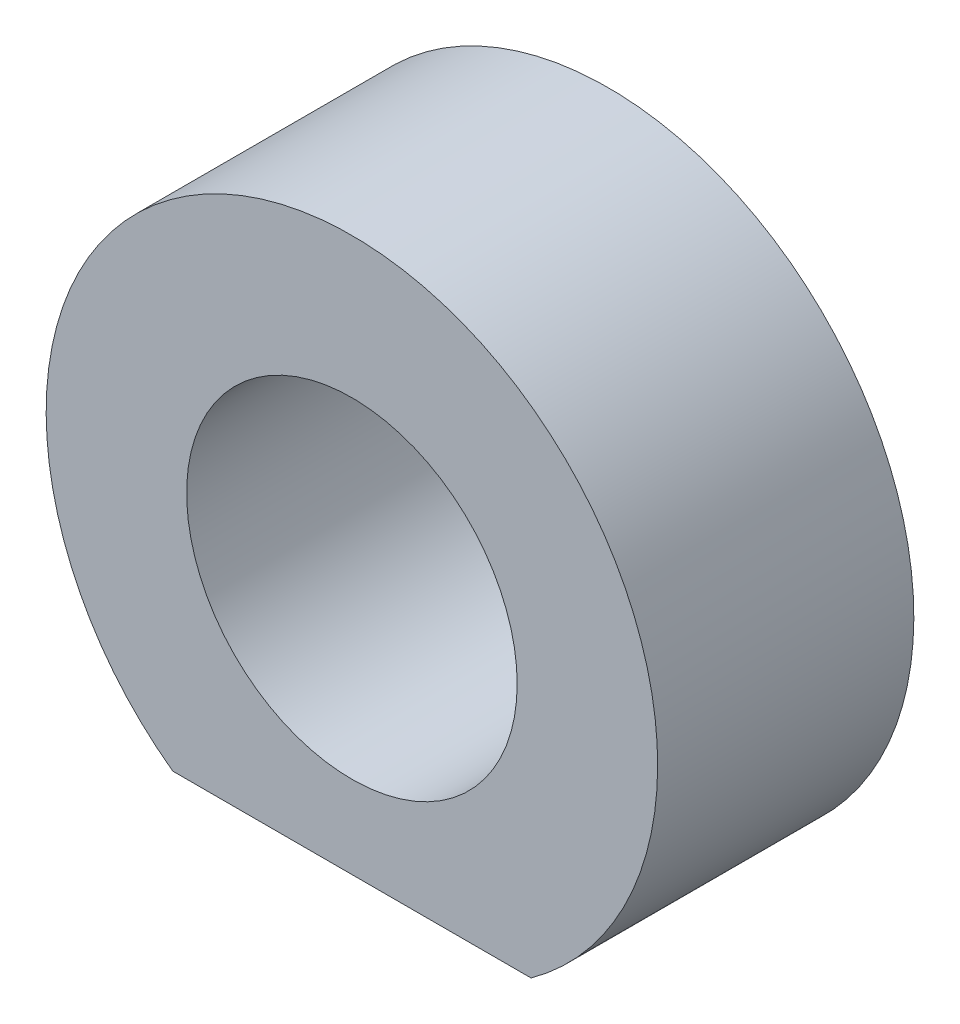
SolidWorks part; units mm, degrees
ref_plane "Front Plane" through (0, 0, 0) normal (0, 0, 1) x (1, 0, 0)
ref_plane "Top Plane" through (0, 0, 0) normal (0, 1, 0) x (1, 0, 0)
ref_plane "Right Plane" through (0, 0, 0) normal (1, 0, 0) x (0, 0, -1)
sketch "Sketch1" plane through (0, 0, 0) normal (0, 0, 1) x (1, 0, 0)
  line L0 (0, -23.3211) -> (0, -18.5) construction
  line L1 (-24.2602, 0) -> (25.6689, 0) construction
  line L2 (-10.84, -14.9915) -> (10.84, -14.9915)
  line L3 (0, -14.9915) -> (0, 23.3211) construction
  circle A0 centre (0, 0) radius 10
  arc A1 (10.84, -14.9915) -> (-10.84, -14.9915) centre (0, 0) ccw
  point P7 (0, 0)
  dimension "D1" = 20
  dimension "D2" = 37
  dimension "D3" = 21.68
extrude "Boss-Extrude1" add sketch "Sketch1" along normal blind 15.5
hole_wizard "Ø2.0 (2) Diameter Hole1" positions "Sketch3" profile "Sketch4" hole size "Ø2.0" standard "ISO"
sketch "Sketch3" plane through (0, -14.9915, 0) normal (0, -1, 0) x (-1, 0, 0)
  point P0 (0, -7.75)
  dimension "D1" = 7.75
sketch "Sketch4" plane through (0, -14.9915, 7.75) normal (1, 0, 0) x (0, 0, -1)
  line L0 (0, 0) -> (0, 2.6009)
  line L1 (0, 2.6009) -> (1, 2)
  line L2 (1, 2) -> (1, 0)
  line L5 (1, 0) -> (0, 0)
  line L10 (0, 2.6009) -> (-1, 2) construction
  line L11 (0, -6.35) -> (0, 107.95) construction
  dimension "Hole Dia." = 2
  dimension "Hole Depth" = 2
  dimension "Drill Angle" = 118
